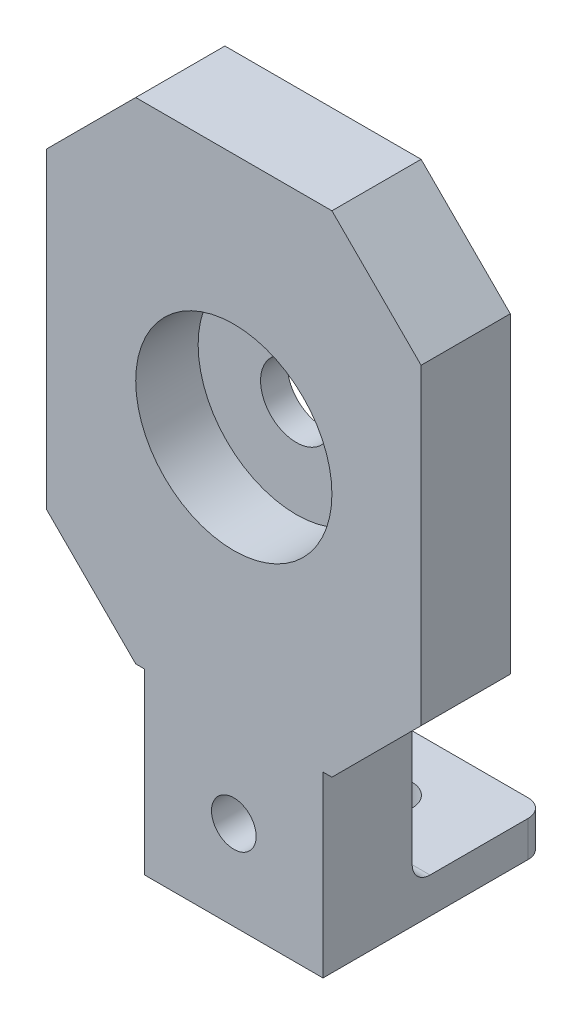
SolidWorks part; units mm, degrees
material "PLA"
ref_plane "Piano frontale" through (0, 0, 0) normal (0, 0, 1) x (1, 0, 0)
ref_plane "Piano superiore" through (0, 0, 0) normal (0, 1, 0) x (1, 0, 0)
ref_plane "Piano destro" through (0, 0, 0) normal (1, 0, 0) x (0, 0, -1)
sketch "Schizzo1" plane through (0, 0, 0) normal (0, 0, 1) x (1, 0, 0)
  line L0 (0, 0) -> (0, -47.5) construction
  line L1 (-10, -47.5) -> (10, -47.5)
  line L2 (-21, -27.5) -> (-21, 27.5)
  line L3 (-21, 27.5) -> (21, 27.5)
  line L4 (21, -27.5) -> (21, 27.5)
  line L5 (-21, -27.5) -> (21, 27.5) construction
  line L6 (-21, 27.5) -> (21, -27.5) construction
  line L7 (-10, -47.5) -> (-10, -27.5)
  line L8 (-10, -27.5) -> (-21, -27.5)
  line L9 (10, -47.5) -> (10, -27.5)
  line L10 (10, -27.5) -> (21, -27.5)
  point P0 (0, 0)
  dimension "D1" = 42
  dimension "D3" = 20
  dimension "D4" = 10
  dimension "D5" = 55
extrude "Estrusione-Estrusione1" add sketch "Schizzo1" along normal blind 10
sketch "Schizzo6" plane through (0, 0, 10) normal (0, 0, 1) x (1, 0, 0)
  line L0 (-10, -47.5) -> (10, -47.5) construction
  line L1 (21, 27.5) -> (-21, 27.5) construction
  circle A0 centre (0, 0) radius 11
  dimension "D1" = 22
  dimension "D2" = 47.5
extrude "Taglio-Estrusione4" cut sketch "Schizzo6" against normal blind 7
sketch "Schizzo7" plane through (0, 0, 3) normal (0, 0, 1) x (1, 0, 0)
  circle A0 centre (0, 0) radius 4
  dimension "D1" = 8
extrude "Taglio-Estrusione5" cut sketch "Schizzo7" against normal through all
chamfer "Smusso2" distance 10 angle 45 4 edges at (-21, -27.5, 5) (21, -27.5, 5) (21, 27.5, 5) (-21, 27.5, 5)
sketch "Schizzo8" plane through (0, 0, 0) normal (0, 0, -1) x (-1, 0, 0)
  line L0 (10, -27.5) -> (10, -47.5) construction
  line L1 (-10, -47.5) -> (10, -47.5)
  line L2 (-10, -47.5) -> (-10, -43.5)
  line L3 (-10, -43.5) -> (10, -43.5)
  line L4 (10, -47.5) -> (10, -43.5)
  dimension "D1" = 4
extrude "Estrusione-Estrusione3" add sketch "Schizzo8" along normal blind 15
sketch "Schizzo9" plane through (0, -43.5, 0) normal (0, 1, 0) x (1, 0, 0)
  line L0 (0, 15) -> (0, 0) construction
  line L1 (-10, 15) -> (10, 15) construction
  line L2 (11, 0) -> (-11, 0) construction
  circle A0 centre (0, 7.5) radius 2.5
  dimension "D1" = 5
  dimension "D3" = 7.5
extrude "Taglio-Estrusione6" cut sketch "Schizzo9" against normal blind 35
fillet "Raccordo1" radius 2 3 edges at (0, -43.5, 0) (-10, -45.5, -15) (10, -45.5, -15)
sketch "Schizzo10" plane through (0, 0, 0) normal (0, 0, -1) x (-1, 0, 0)
  line L0 (-8, -47.5) -> (8, -47.5) construction
  circle A0 centre (0, -37.5) radius 2.5
  dimension "D2" = 5
  dimension "D1" = 10
extrude "Taglio-Estrusione7" cut sketch "Schizzo10" against normal blind 10
